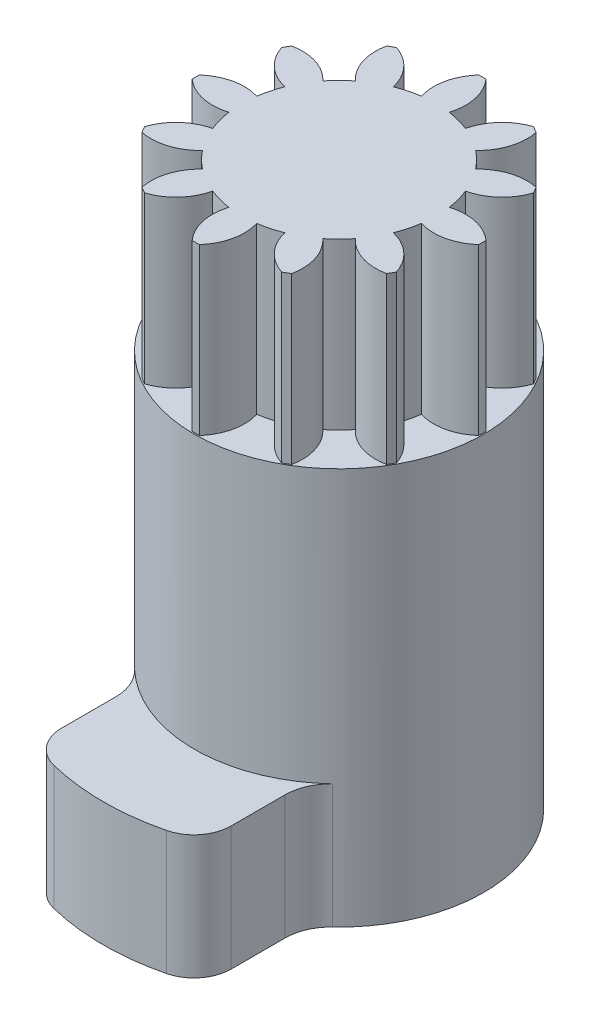
SolidWorks part; units mm, degrees
ref_plane "Front Plane" through (0, 0, 0) normal (0, 0, 1) x (1, 0, 0)
ref_plane "Top Plane" through (0, 0, 0) normal (0, 1, 0) x (1, 0, 0)
ref_plane "Right Plane" through (0, 0, 0) normal (1, 0, 0) x (0, 0, -1)
sketch "Sketch1" plane through (0, 0, 0) normal (0, 1, 0) x (1, 0, 0)
  circle A0 centre (0, 0) radius 17.5
  dimension "D1" = 35
extrude "Boss-Extrude1" add sketch "Sketch1" along normal offset from surface (48 mm away) 5
sketch "Sketch2" plane through (0, 0, 0) normal (0, -1, 0) x (1, 0, 0)
  line L0 (0, 0) -> (50.5654, 0) construction
ref_plane "Plane1" through (17.5, 0, 0) normal (1, 0, 0) x (0, 0, -1)
sketch "Sketch4" plane through (0, 0, 0) normal (0, -1, 0) x (1, 0, 0)
  line L11 (10.25, 23.3043) -> (10.25, 16.7612)
  line L12 (-10.25, 16.7612) -> (-10.25, 23.3043)
  line L13 (10.25, 23.3043) -> (10.25, 16.7612)
  line L14 (-10.25, 16.7612) -> (-10.25, 23.3043)
  circle A5 centre (0, 0) radius 17.5 construction
  arc A6 (11.9837, 12.7531) -> (-11.9837, 12.7531) centre (0, 0) ccw
  arc A10 (10.25, 16.7612) -> (11.9837, 12.7531) centre (15.75, 16.7612) ccw
  arc A11 (10.25, 23.3043) -> (6.828, 27.6733) centre (5.75, 23.3043) ccw
  arc A12 (6.828, 27.6733) -> (-6.828, 27.6733) centre (0, 0) ccw
  arc A13 (-6.828, 27.6733) -> (-10.25, 23.3043) centre (-5.75, 23.3043) ccw
  arc A14 (-11.9837, 12.7531) -> (-10.25, 16.7612) centre (-15.75, 16.7612) ccw
  arc A15 (10.25, 16.7612) -> (11.9837, 12.7531) centre (15.75, 16.7612) ccw
  arc A16 (10.25, 23.3043) -> (6.828, 27.6733) centre (5.75, 23.3043) ccw
  arc A17 (6.828, 27.6733) -> (-6.828, 27.6733) centre (0, 0) ccw
  arc A18 (-6.828, 27.6733) -> (-10.25, 23.3043) centre (-5.75, 23.3043) ccw
  arc A19 (-11.9837, 12.7531) -> (-10.25, 16.7612) centre (-15.75, 16.7612) ccw
  dimension "D1" = 0.5
extrude "Boss-Extrude2" add sketch "Sketch4" against normal blind 15
sketch "Sketch6" plane through (0, 48, 0) normal (0, 1, 0) x (1, 0, 0)
  arc A96 (11.6416, -1.6851) -> (17.3299, -0.4402) centre (13.3779, 3.9992) ccw
  arc A97 (10.9244, -4.3614) -> (11.6416, -1.6851) centre (0, 0) ccw
  arc A98 (15.2282, -8.2838) -> (10.9244, -4.3614) centre (9.586, -10.1524) ccw
  arc A99 (14.7881, -9.0462) -> (15.2282, -8.2838) centre (0, 0) ccw
  arc A100 (9.2393, -7.2801) -> (14.7881, -9.0462) centre (13.5852, -3.2255) ccw
  arc A101 (7.2801, -9.2393) -> (9.2393, -7.2801) centre (0, 0) ccw
  arc A102 (9.0462, -14.7881) -> (7.2801, -9.2393) centre (3.2255, -13.5852) ccw
  arc A103 (8.2838, -15.2282) -> (9.0462, -14.7881) centre (0, 0) ccw
  arc A104 (4.3614, -10.9244) -> (8.2838, -15.2282) centre (10.1524, -9.586) ccw
  arc A105 (1.6851, -11.6416) -> (4.3614, -10.9244) centre (0, 0) ccw
  arc A106 (0.4402, -17.3299) -> (1.6851, -11.6416) centre (-3.9992, -13.3779) ccw
  arc A107 (-0.4402, -17.3299) -> (0.4402, -17.3299) centre (0, 0) ccw
  arc A108 (-1.6851, -11.6416) -> (-0.4402, -17.3299) centre (3.9992, -13.3779) ccw
  arc A109 (-4.3614, -10.9244) -> (-1.6851, -11.6416) centre (0, 0) ccw
  arc A110 (-8.2838, -15.2282) -> (-4.3614, -10.9244) centre (-10.1524, -9.586) ccw
  arc A111 (-9.0462, -14.7881) -> (-8.2838, -15.2282) centre (0, 0) ccw
  arc A112 (-7.2801, -9.2393) -> (-9.0462, -14.7881) centre (-3.2255, -13.5852) ccw
  arc A113 (-9.2393, -7.2801) -> (-7.2801, -9.2393) centre (0, 0) ccw
  arc A114 (-14.7881, -9.0462) -> (-9.2393, -7.2801) centre (-13.5852, -3.2255) ccw
  arc A115 (-15.2282, -8.2838) -> (-14.7881, -9.0462) centre (0, 0) ccw
  arc A116 (-10.9244, -4.3614) -> (-15.2282, -8.2838) centre (-9.586, -10.1524) ccw
  arc A117 (-11.6416, -1.6851) -> (-10.9244, -4.3614) centre (0, 0) ccw
  arc A118 (-17.3299, -0.4402) -> (-11.6416, -1.6851) centre (-13.3779, 3.9992) ccw
  arc A119 (-17.3299, 0.4402) -> (-17.3299, -0.4402) centre (0, 0) ccw
  arc A120 (-11.6416, 1.6851) -> (-17.3299, 0.4402) centre (-13.3779, -3.9992) ccw
  arc A121 (-10.9244, 4.3614) -> (-11.6416, 1.6851) centre (0, 0) ccw
  arc A122 (-15.2282, 8.2838) -> (-10.9244, 4.3614) centre (-9.586, 10.1524) ccw
  arc A123 (-14.7881, 9.0462) -> (-15.2282, 8.2838) centre (0, 0) ccw
  arc A124 (-9.2393, 7.2801) -> (-14.7881, 9.0462) centre (-13.5852, 3.2255) ccw
  arc A125 (-7.2801, 9.2393) -> (-9.2393, 7.2801) centre (0, 0) ccw
  arc A126 (-9.0462, 14.7881) -> (-7.2801, 9.2393) centre (-3.2255, 13.5852) ccw
  arc A127 (-8.2838, 15.2282) -> (-9.0462, 14.7881) centre (0, 0) ccw
  arc A128 (-4.3614, 10.9244) -> (-8.2838, 15.2282) centre (-10.1524, 9.586) ccw
  arc A129 (-1.6851, 11.6416) -> (-4.3614, 10.9244) centre (0, 0) ccw
  arc A130 (-0.4402, 17.3299) -> (-1.6851, 11.6416) centre (3.9992, 13.3779) ccw
  arc A131 (0.4402, 17.3299) -> (-0.4402, 17.3299) centre (0, 0) ccw
  arc A132 (1.6851, 11.6416) -> (0.4402, 17.3299) centre (-3.9992, 13.3779) ccw
  arc A133 (4.3614, 10.9244) -> (1.6851, 11.6416) centre (0, 0) ccw
  arc A134 (8.2838, 15.2282) -> (4.3614, 10.9244) centre (10.1524, 9.586) ccw
  arc A135 (9.0462, 14.7881) -> (8.2838, 15.2282) centre (0, 0) ccw
  arc A136 (7.2801, 9.2393) -> (9.0462, 14.7881) centre (3.2255, 13.5852) ccw
  arc A137 (9.2393, 7.2801) -> (7.2801, 9.2393) centre (0, 0) ccw
  arc A138 (14.7881, 9.0462) -> (9.2393, 7.2801) centre (13.5852, 3.2255) ccw
  arc A139 (15.2282, 8.2838) -> (14.7881, 9.0462) centre (0, 0) ccw
  arc A140 (10.9244, 4.3614) -> (15.2282, 8.2838) centre (9.586, 10.1524) ccw
  arc A141 (11.6416, 1.6851) -> (10.9244, 4.3614) centre (0, 0) ccw
  arc A142 (17.3299, 0.4402) -> (11.6416, 1.6851) centre (13.3779, -3.9992) ccw
  arc A143 (17.3299, -0.4402) -> (17.3299, 0.4402) centre (0, 0) ccw
extrude "Boss-Extrude3" add sketch "Sketch6" along normal blind 20
sketch "Sketch7" plane through (0, 68, 0) normal (0, 1, 0) x (1, 0, 0)
  point P0 (0, 0)
